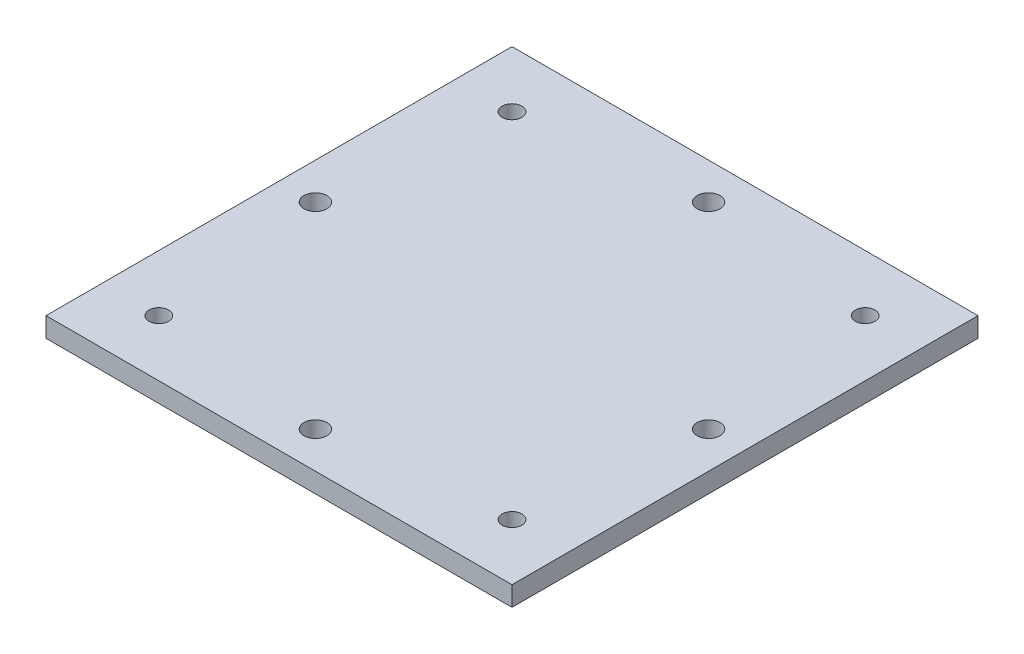
SolidWorks part; units mm, degrees
ref_plane "Front Plane" through (0, 0, 0) normal (0, 0, 1) x (1, 0, 0)
ref_plane "Top Plane" through (0, 0, 0) normal (0, 1, 0) x (1, 0, 0)
ref_plane "Right Plane" through (0, 0, 0) normal (1, 0, 0) x (0, 0, -1)
sketch "Sketch2" plane through (0, 0, 0) normal (0, 1, 0) x (1, 0, 0)
  line L0 (-26.9494, 26.9494) -> (26.9494, 26.9494) construction
  line L1 (35.56, -35.56) -> (-35.56, -35.56)
  line L2 (35.56, -35.56) -> (35.56, 35.56)
  line L3 (35.56, 35.56) -> (-35.56, 35.56)
  line L4 (-35.56, -35.56) -> (-35.56, 35.56)
  line L5 (35.56, -35.56) -> (-35.56, 35.56) construction
  line L6 (35.56, 35.56) -> (-35.56, -35.56) construction
  line L7 (-26.9494, -26.9494) -> (26.9494, -26.9494) construction
  line L8 (-26.9494, 26.9494) -> (-26.9494, -26.9494) construction
  line L9 (26.9494, 26.9494) -> (26.9494, -26.9494) construction
  line L10 (0, 26.9494) -> (0, -26.9494) construction
  circle A0 centre (0, 30) radius 1.7526
  circle A1 centre (-30, 0) radius 1.7526
  circle A2 centre (30, 0) radius 1.7526
  circle A3 centre (0, -30) radius 1.7526
  circle A4 centre (0, 0) radius 30 construction
  circle A8 centre (26.9494, 26.9494) radius 1.5
  circle A9 centre (-26.9494, 26.9494) radius 1.5
  circle A10 centre (26.9494, -26.9494) radius 1.5
  circle A11 centre (-26.9494, -26.9494) radius 1.5
  point P0 (0, 0)
  point P19 (0, 0)
  point P22 (0, 0)
  dimension "D3" = 60
  dimension "D6" = 3
  dimension "D2" = 3.5052
  dimension "D1" = 71.12
  dimension "D4" = 53.8988
extrude "Boss-Extrude1" add sketch "Sketch2" along normal blind 3
